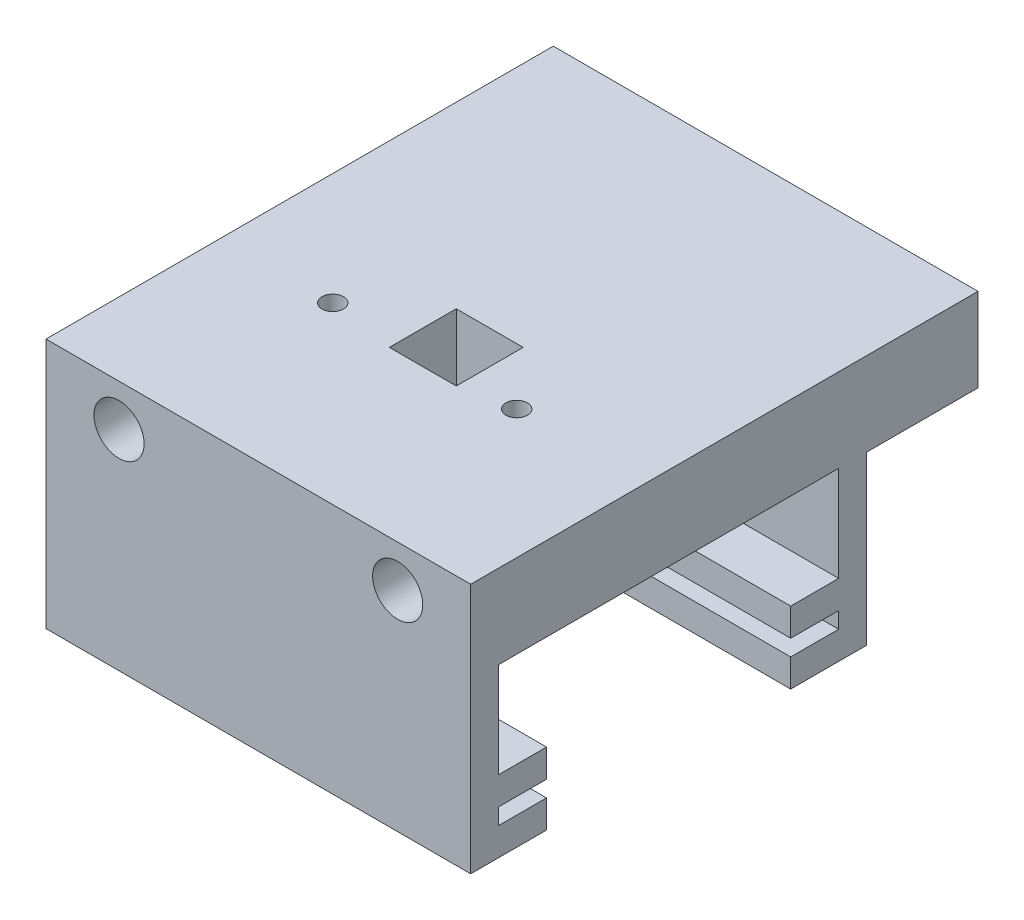
SolidWorks part; units mm, degrees
ref_plane "Front Plane" through (0, 0, 0) normal (0, 0, 1) x (1, 0, 0)
ref_plane "Top Plane" through (0, 0, 0) normal (0, 1, 0) x (1, 0, 0)
ref_plane "Right Plane" through (0, 0, 0) normal (1, 0, 0) x (0, 0, -1)
sketch "Sketch2" plane through (0, 0, 0) normal (0, 0, 1) x (1, 0, 0)
  line L0 (-22, 1.15) -> (3, 1.15) construction
  line L1 (-35.1, 8.65) -> (41.1, 8.65)
  line L2 (-35.1, 8.65) -> (-35.1, -6.35)
  line L3 (-35.1, -6.35) -> (41.1, -6.35)
  line L4 (41.1, 8.65) -> (41.1, -6.35)
  line L12 (3, 1.15) -> (3, 14.1161) construction
  line L13 (3, 1.15) -> (28, 1.15) construction
  circle A0 centre (-22, 1.15) radius 3.9688
  circle A1 centre (28, 1.15) radius 3.9687
  point P2 (3, 8.65)
  dimension "D1" = 7.9375
  dimension "D2" = 7.9375
  dimension "D3" = 15
  dimension "D4" = 50
  dimension "D6" = 76.2
extrude "Top + failed holes" add sketch "Sketch2" against normal blind 71.02
sketch "Sketch8" plane through (-35.1, 0, 0) normal (-1, 0, 0) x (0, 0, 1)
  line L0 (-56.45, 9.45) -> (-56.45, 8.75)
  line L1 (-57.25, 4.65) -> (-17.25, 4.65)
  line L2 (-57.25, 4.65) -> (-57.25, 9.45)
  line L3 (-57.15, 9.55) -> (-56.55, 9.55)
  line L4 (-17.25, 4.65) -> (-17.25, 9.45)
  line L5 (-56.35, 8.65) -> (-55.35, 8.65)
  line L6 (-18.05, 9.45) -> (-18.05, 8.75)
  line L7 (-17.95, 9.55) -> (-17.35, 9.55)
  line L8 (-55.25, 8.75) -> (-55.25, 9.45)
  line L9 (-55.15, 9.55) -> (-54.55, 9.55)
  line L10 (-54.45, 9.45) -> (-54.45, 8.75)
  line L11 (-53.25, 8.75) -> (-53.25, 9.45)
  line L12 (-53.15, 9.55) -> (-52.55, 9.55)
  line L13 (-52.45, 9.45) -> (-52.45, 8.75)
  line L14 (-51.25, 8.75) -> (-51.25, 9.45)
  line L15 (-51.15, 9.55) -> (-50.55, 9.55)
  line L16 (-50.45, 9.45) -> (-50.45, 8.75)
  line L17 (-49.25, 8.75) -> (-49.25, 9.45)
  line L18 (-49.15, 9.55) -> (-48.55, 9.55)
  line L19 (-48.45, 9.45) -> (-48.45, 8.75)
  line L20 (-47.25, 8.75) -> (-47.25, 9.45)
  line L21 (-47.15, 9.55) -> (-46.55, 9.55)
  line L22 (-46.45, 9.45) -> (-46.45, 8.75)
  line L23 (-45.25, 8.75) -> (-45.25, 9.45)
  line L24 (-45.15, 9.55) -> (-44.55, 9.55)
  line L25 (-44.45, 9.45) -> (-44.45, 8.75)
  line L26 (-44.35, 8.65) -> (-30.15, 8.65)
  line L27 (-46.35, 8.65) -> (-45.35, 8.65)
  line L28 (-48.35, 8.65) -> (-47.35, 8.65)
  line L29 (-50.35, 8.65) -> (-49.35, 8.65)
  line L30 (-52.35, 8.65) -> (-51.35, 8.65)
  line L31 (-54.35, 8.65) -> (-53.35, 8.65)
  line L32 (-20.05, 9.45) -> (-20.05, 8.75)
  line L33 (-19.95, 9.55) -> (-19.35, 9.55)
  line L34 (-19.25, 8.75) -> (-19.25, 9.45)
  line L35 (-22.05, 9.45) -> (-22.05, 8.75)
  line L36 (-21.95, 9.55) -> (-21.35, 9.55)
  line L37 (-21.25, 8.75) -> (-21.25, 9.45)
  line L38 (-24.05, 9.45) -> (-24.05, 8.75)
  line L39 (-23.95, 9.55) -> (-23.35, 9.55)
  line L40 (-23.25, 8.75) -> (-23.25, 9.45)
  line L41 (-26.05, 9.45) -> (-26.05, 8.75)
  line L42 (-25.95, 9.55) -> (-25.35, 9.55)
  line L43 (-25.25, 8.75) -> (-25.25, 9.45)
  line L44 (-28.05, 9.45) -> (-28.05, 8.75)
  line L45 (-27.95, 9.55) -> (-27.35, 9.55)
  line L46 (-27.25, 8.75) -> (-27.25, 9.45)
  line L47 (-30.05, 9.45) -> (-30.05, 8.75)
  line L48 (-29.95, 9.55) -> (-29.35, 9.55)
  line L49 (-29.25, 8.75) -> (-29.25, 9.45)
  line L50 (-29.15, 8.65) -> (-28.15, 8.65)
  line L51 (-27.15, 8.65) -> (-26.15, 8.65)
  line L52 (-25.15, 8.65) -> (-24.15, 8.65)
  line L53 (-23.15, 8.65) -> (-22.15, 8.65)
  line L54 (-21.15, 8.65) -> (-20.15, 8.65)
  line L55 (-19.15, 8.65) -> (-18.15, 8.65)
  line L56 (-35.51, 8.65) -> (-35.51, 28.1232) construction
  line L57 (-71.02, 8.65) -> (0, 8.65) construction
  arc A0 (-17.35, 9.55) -> (-17.25, 9.45) centre (-17.35, 9.45) cw
  arc A1 (-18.05, 9.45) -> (-17.95, 9.55) centre (-17.95, 9.45) cw
  arc A2 (-18.15, 8.65) -> (-18.05, 8.75) centre (-18.15, 8.75) ccw
  arc A3 (-19.15, 8.65) -> (-19.25, 8.75) centre (-19.15, 8.75) cw
  arc A4 (-19.35, 9.55) -> (-19.25, 9.45) centre (-19.35, 9.45) cw
  arc A5 (-20.05, 9.45) -> (-19.95, 9.55) centre (-19.95, 9.45) cw
  arc A6 (-20.05, 8.75) -> (-20.15, 8.65) centre (-20.15, 8.75) cw
  arc A7 (-21.15, 8.65) -> (-21.25, 8.75) centre (-21.15, 8.75) cw
  arc A8 (-21.35, 9.55) -> (-21.25, 9.45) centre (-21.35, 9.45) cw
  arc A9 (-22.05, 9.45) -> (-21.95, 9.55) centre (-21.95, 9.45) cw
  arc A10 (-22.05, 8.75) -> (-22.15, 8.65) centre (-22.15, 8.75) cw
  arc A11 (-23.25, 8.75) -> (-23.15, 8.65) centre (-23.15, 8.75) ccw
  arc A12 (-23.35, 9.55) -> (-23.25, 9.45) centre (-23.35, 9.45) cw
  arc A13 (-24.05, 9.45) -> (-23.95, 9.55) centre (-23.95, 9.45) cw
  arc A14 (-24.05, 8.75) -> (-24.15, 8.65) centre (-24.15, 8.75) cw
  arc A15 (-25.25, 8.75) -> (-25.15, 8.65) centre (-25.15, 8.75) ccw
  arc A16 (-25.35, 9.55) -> (-25.25, 9.45) centre (-25.35, 9.45) cw
  arc A17 (-26.05, 9.45) -> (-25.95, 9.55) centre (-25.95, 9.45) cw
  arc A18 (-26.05, 8.75) -> (-26.15, 8.65) centre (-26.15, 8.75) cw
  arc A19 (-27.25, 8.75) -> (-27.15, 8.65) centre (-27.15, 8.75) ccw
  arc A20 (-27.35, 9.55) -> (-27.25, 9.45) centre (-27.35, 9.45) cw
  arc A21 (-28.05, 9.45) -> (-27.95, 9.55) centre (-27.95, 9.45) cw
  arc A22 (-28.05, 8.75) -> (-28.15, 8.65) centre (-28.15, 8.75) cw
  arc A23 (-29.25, 8.75) -> (-29.15, 8.65) centre (-29.15, 8.75) ccw
  arc A24 (-29.35, 9.55) -> (-29.25, 9.45) centre (-29.35, 9.45) cw
  arc A25 (-30.05, 9.45) -> (-29.95, 9.55) centre (-29.95, 9.45) cw
  arc A26 (-30.05, 8.75) -> (-30.15, 8.65) centre (-30.15, 8.75) cw
  arc A27 (-44.45, 8.75) -> (-44.35, 8.65) centre (-44.35, 8.75) ccw
  arc A28 (-44.55, 9.55) -> (-44.45, 9.45) centre (-44.55, 9.45) cw
  arc A29 (-45.25, 8.75) -> (-45.35, 8.65) centre (-45.35, 8.75) cw
  arc A30 (-45.25, 9.45) -> (-45.15, 9.55) centre (-45.15, 9.45) cw
  arc A31 (-46.45, 8.75) -> (-46.35, 8.65) centre (-46.35, 8.75) ccw
  arc A32 (-46.55, 9.55) -> (-46.45, 9.45) centre (-46.55, 9.45) cw
  arc A33 (-47.25, 9.45) -> (-47.15, 9.55) centre (-47.15, 9.45) cw
  arc A34 (-47.25, 8.75) -> (-47.35, 8.65) centre (-47.35, 8.75) cw
  arc A35 (-48.45, 8.75) -> (-48.35, 8.65) centre (-48.35, 8.75) ccw
  arc A36 (-48.55, 9.55) -> (-48.45, 9.45) centre (-48.55, 9.45) cw
  arc A37 (-49.25, 8.75) -> (-49.35, 8.65) centre (-49.35, 8.75) cw
  arc A38 (-49.25, 9.45) -> (-49.15, 9.55) centre (-49.15, 9.45) cw
  arc A39 (-50.45, 8.75) -> (-50.35, 8.65) centre (-50.35, 8.75) ccw
  arc A40 (-50.55, 9.55) -> (-50.45, 9.45) centre (-50.55, 9.45) cw
  arc A41 (-51.25, 8.75) -> (-51.35, 8.65) centre (-51.35, 8.75) cw
  arc A42 (-51.25, 9.45) -> (-51.15, 9.55) centre (-51.15, 9.45) cw
  arc A43 (-52.45, 8.75) -> (-52.35, 8.65) centre (-52.35, 8.75) ccw
  arc A44 (-52.55, 9.55) -> (-52.45, 9.45) centre (-52.55, 9.45) cw
  arc A45 (-53.25, 8.75) -> (-53.35, 8.65) centre (-53.35, 8.75) cw
  arc A46 (-53.25, 9.45) -> (-53.15, 9.55) centre (-53.15, 9.45) cw
  arc A47 (-54.45, 8.75) -> (-54.35, 8.65) centre (-54.35, 8.75) ccw
  arc A48 (-54.55, 9.55) -> (-54.45, 9.45) centre (-54.55, 9.45) cw
  arc A49 (-55.25, 8.75) -> (-55.35, 8.65) centre (-55.35, 8.75) cw
  arc A50 (-55.25, 9.45) -> (-55.15, 9.55) centre (-55.15, 9.45) cw
  arc A51 (-56.45, 8.75) -> (-56.35, 8.65) centre (-56.35, 8.75) ccw
  arc A52 (-56.45, 9.45) -> (-56.55, 9.55) centre (-56.55, 9.45) ccw
  arc A53 (-57.25, 9.45) -> (-57.15, 9.55) centre (-57.15, 9.45) cw
  point P165 (-37.25, 8.65)
  dimension "D1" = 0.1
  dimension "D2" = 14.2
sketch "Sketch13" plane through (0, 8.65, 0) normal (0, 1, 0) x (1, 0, 0)
  line L0 (41.1, 71.02) -> (41.1, 0) construction
  line L1 (-35.1, 71.02) -> (41.1, 71.02)
  line L3 (-30.1, 66.02) -> (41.1, 66.02)
  line L4 (41.1, 71.02) -> (41.1, 66.02)
  line L5 (-35.1, 0) -> (41.1, 0) construction
  line L7 (-35.1, 71.02) -> (-35.1, 0)
  line L9 (-30.1, 66.02) -> (-30.1, 5)
  line L11 (-35.1, 0) -> (41.1, 0)
  line L13 (-30.1, 5) -> (41.1, 5)
  line L14 (41.1, 0) -> (41.1, 5)
  dimension "D1" = 5
  dimension "D2" = 5
  dimension "D3" = 5
extrude "Walls" add sketch "Sketch13" against normal blind 45
sketch "Sketch14" plane through (0, 0, 0) normal (0, 0, 1) x (1, 0, 0)
  line L0 (-22, 1.15) -> (3, 1.15) construction
  line L1 (-35.1, 8.65) -> (41.1, 8.65)
  line L2 (-35.1, 8.65) -> (-35.1, -6.35)
  line L3 (-35.1, -6.35) -> (41.1, -6.35)
  line L4 (41.1, 8.65) -> (41.1, -6.35)
  line L5 (3, 1.15) -> (3, 14.1161) construction
  line L6 (3, 1.15) -> (28, 1.15) construction
  circle A0 centre (-22, 1.15) radius 4.5
  circle A1 centre (28, 1.15) radius 4.5
  point P2 (3, 8.65)
  dimension "D1" = 9
  dimension "D2" = 9
  dimension "D3" = 15
  dimension "D4" = 50
  dimension "D5" = 76.2
extrude "Rod Holes" cut sketch "Sketch14" against normal through all contours A0 | A1
sketch "Sketch15" plane through (0, -36.35, 0) normal (0, -1, 0) x (1, 0, 0)
  line L0 (-35.1, -35.51) -> (41.1, -35.51) construction
  line L1 (-35.1, 0) -> (41.1, 0)
  line L2 (-35.1, 0) -> (-35.1, -71.02)
  line L3 (-35.1, -71.02) -> (41.1, -71.02)
  line L4 (41.1, 0) -> (41.1, -71.02)
  line L5 (-35.1, 0) -> (41.1, 0)
  line L6 (-35.1, 0) -> (-35.1, -12.0833)
  line L8 (41.1, 0) -> (41.1, -12.0833)
  line L9 (-35.1, -71.02) -> (41.1, -71.02)
  line L10 (-35.1, -71.02) -> (-35.1, -57.415)
  line L11 (-35.1, -57.415) -> (41.1, -57.415)
  line L12 (41.1, -71.02) -> (41.1, -57.415)
  line L13 (-35.1, -13.605) -> (41.1, -13.605)
  line L14 (41.1, 0) -> (41.1, -13.605)
  line L15 (-35.1, 0) -> (41.1, 0)
  line L16 (-35.1, 0) -> (-35.1, -13.605)
  line M1 (41.1, -71.02) -> (41.1, -66.02)
  line M2 (41.1, -66.02) -> (-30.1, -66.02)
  line M3 (-30.1, -66.02) -> (-30.1, -5)
  line M4 (-30.1, -5) -> (41.1, -5)
  line M5 (41.1, -5) -> (41.1, 0)
  line M6 (41.1, 0) -> (-35.1, 0)
  line M7 (-35.1, 0) -> (-35.1, -71.02)
  line M8 (-35.1, -71.02) -> (41.1, -71.02)
  dimension "D1" = 43.81
extrude "Base hold syringe" add sketch "Sketch15" against normal blind 5 contours L13 L4 M3 M4 | L2 L13 M3 M4 M5 M6 M7 | L11 L4 M3 M2 | L11 M7 M8 M1 M2 M3
sketch "Sketch16" plane through (0, 0, -71.02) normal (0, 0, -1) x (-1, 0, 0)
  line L0 (-28, 1.15) -> (-3, 1.15) construction
  line L1 (-41.1, 8.65) -> (35.1, 8.65)
  line L2 (-41.1, 8.65) -> (-41.1, -6.35)
  line L3 (-41.1, -6.35) -> (35.1, -6.35)
  line L4 (35.1, 8.65) -> (35.1, -6.35)
  line L5 (-3, 1.15) -> (-3, 14.1161) construction
  line L6 (-3, 1.15) -> (22, 1.15) construction
  circle A0 centre (-28, 1.15) radius 4.5
  circle A1 centre (22, 1.15) radius 4.5
  point P2 (-3, 8.65)
  dimension "D1" = 9
  dimension "D2" = 9
  dimension "D3" = 15
  dimension "D4" = 50
  dimension "D5" = 76.2
extrude "extension for motor" add sketch "Sketch16" along normal blind 20
sketch "Sketch6" plane through (0, 8.65, 0) normal (0, 1, 0) x (1, 0, 0)
  line L0 (41.1, 71.02) -> (-35.1, 71.02) construction
  line L6 (3, 41.51) -> (3, 29.51) construction
  line L7 (41.1, 71.02) -> (-35.1, 71.02)
  line L8 (-35.1, 0) -> (41.1, 0) construction
  line L17 (3, 71.02) -> (3, 0) construction
  line L18 (-35.1, 0) -> (41.1, 0)
  line L20 (38.47, 48.51) -> (38.47, 21.19)
  line L27 (9, 41.51) -> (-3, 41.51)
  line L28 (9, 29.51) -> (9, 41.51)
  line L29 (-3, 29.51) -> (9, 29.51)
  line L30 (-27.57, 48.51) -> (38.47, 48.51)
  line L31 (-27.57, 21.19) -> (-27.57, 48.51)
  line L32 (38.47, 21.19) -> (-27.57, 21.19)
  line L33 (-3, 41.51) -> (-3, 29.51)
  line L34 (18, 41.51) -> (18, 21.19) construction
  line L35 (-15, 41.51) -> (-15, 21.19) construction
  line L36 (-15, 41.51) -> (18, 41.51) construction
  circle A7 centre (18, 31.35) radius 1.925
  circle A8 centre (-15, 31.35) radius 1.925
  circle A9 centre (3, 35.51) radius 21.905
  point P0 (3, 35.51)
  point P1 (3, 35.51)
  point P4 (-15, 31.35)
  point P5 (18, 31.35)
  point P11 (11.9104, 37.25)
  point P13 (3, 71.02)
  dimension "D3" = 3.85
  dimension "D4" = 43.81
  dimension "D5" = 3.85
  dimension "D10" = 9
  dimension "D2" = 12
  dimension "D6" = 12
  dimension "D7" = 12
  dimension "D8" = 66.04
  dimension "D9" = 27.32
  dimension "D12" = 24.57
  dimension "D14" = 20.32
  dimension "D15" = 7
extrude "Track and screws" cut sketch "Sketch6" against normal up to next
sketch "Sketch17" plane through (0, 8.65, 0) normal (0, 1, 0) x (1, 0, 0)
  line L3 (-2.03, 88.71) -> (41.1, 88.71)
  line L4 (-2.03, 88.71) -> (-2.03, 91.02)
  line L5 (-2.03, 91.02) -> (41.1, 91.02)
  line L6 (41.1, 88.71) -> (41.1, 91.02)
  line L7 (-35.1, 91.02) -> (41.1, 91.02) construction
  line L8 (41.1, 91.02) -> (41.1, 0) construction
  line L9 (9, 41.51) -> (-3, 41.51) construction
  dimension "D2" = 47.2
sketch "Sketch18" plane through (41.1, 0, 0) normal (1, 0, 0) x (0, 0, -1)
  line L0 (5, -31.35) -> (5, -6.35) construction
  line L1 (5, -28.45) -> (13.605, -28.45)
  line L2 (5, -28.45) -> (5, -23.45)
  line L3 (5, -23.45) -> (13.605, -23.45)
  line L4 (13.605, -28.45) -> (13.605, -23.45)
  line L5 (66.02, -31.35) -> (66.02, -6.35) construction
  line L6 (66.02, -28.45) -> (57.415, -28.45)
  line L7 (66.02, -28.45) -> (66.02, -23.45)
  line L8 (66.02, -23.45) -> (57.415, -23.45)
  line L9 (57.415, -28.45) -> (57.415, -23.45)
  line L10 (5, -31.35) -> (13.605, -31.35) construction
  line L11 (13.605, -31.35) -> (13.605, -36.35) construction
  line L12 (57.415, -36.35) -> (57.415, -31.35) construction
  dimension "D1" = 2.9
  dimension "D2" = 5
extrude "Secure syring" add sketch "Sketch18" against normal up to next
ref_plane "Plane1" through (-35.1, 8.65, -91.02) normal (0, 0, 1) x (1, 0, 0)
sketch "Sketch21" plane through (-35.1, 0, 0) normal (-1, 0, 0) x (0, 0, 1)
  line L0 (-91.02, 8.65) -> (0, 8.65) construction
  line L1 (-91.02, 8.65) -> (0, 8.65)
  line L2 (-71.02, -18.6219) -> (0, -18.6219) construction
  line L3 (-35.51, -18.6219) -> (-35.51, -13.8018) construction
  line L4 (-45.51, -18.6219) -> (-25.51, -18.6219) construction
  line L5 (-45.51, -8.3338) -> (-25.51, -8.3338)
  line L6 (-45.51, -28.91) -> (-25.51, -28.91)
  line L8 (-71.02, -36.35) -> (0, -36.35)
  line L9 (0, -36.35) -> (0, 8.65)
  line L10 (0, 8.65) -> (-91.02, 8.65)
  line L11 (-91.02, 8.65) -> (-91.02, -6.35)
  line L12 (-91.02, -6.35) -> (-71.02, -6.35)
  line L13 (-71.02, -6.35) -> (-71.02, -36.35)
  line L14 (-71.02, -36.35) -> (0, -36.35)
  line L15 (0, -36.35) -> (0, 8.65)
  line L16 (0, 8.65) -> (-91.02, 8.65)
  line L17 (-91.02, 8.65) -> (-91.02, -6.35)
  line L18 (-91.02, -6.35) -> (-71.02, -6.35)
  line L19 (-71.02, -6.35) -> (-71.02, -36.35)
  arc A0 (-45.51, -8.3338) -> (-45.51, -28.91) centre (-45.51, -18.6219) ccw
  arc A1 (-25.51, -28.91) -> (-25.51, -8.3338) centre (-25.51, -18.6219) ccw
  point P8 (-45.51, -18.6219)
  point P10 (-25.51, -18.6219)
  point P14 (-35.51, -18.6219)
  dimension "D2" = 20
  dimension "D1" = 0
extrude "Cut-Extrude1" cut sketch "Sketch21" against normal up to next contours L6 A1 L5 A0
sketch "Sketch22" plane through (0, -36.35, 0) normal (0, -1, 0) x (1, 0, 0)
  line L0 (9, -41.51) -> (-3, -41.51) construction
  line L1 (9, -29.51) -> (9, -41.51) construction
  line L2 (9, -41.51) -> (-3, -41.51)
  line L3 (9, -29.51) -> (9, -41.51)
  line L4 (9, -41.51) -> (9, -29.51)
  line L5 (-3, -41.51) -> (9, -41.51)
  line L6 (-3, -29.51) -> (-3, -41.51)
  line L7 (9, -29.51) -> (-3, -29.51)
  line L8 (9, -41.51) -> (9, -29.51)
  line L9 (-3, -41.51) -> (9, -41.51)
  line L10 (-3, -29.51) -> (-3, -41.51)
  line L11 (9, -29.51) -> (-3, -29.51)
  line L12 (3, -29.51) -> (3, -41.51) construction
  line L13 (-19, -57.415) -> (-19, -13.605)
  line L14 (-19, -13.605) -> (-30.1, -13.605)
  line L16 (-30.1, -57.415) -> (-19, -57.415)
  line L17 (-30.1, -13.605) -> (-30.1, -57.415) construction
  line L18 (-30.1, -13.605) -> (-30.1, -57.415)
  line L19 (-30.1, -13.605) -> (41.1, -13.605) construction
  line L20 (-30.1, -57.415) -> (41.1, -57.415) construction
  circle A0 centre (3, -35.51) radius 22
  point P14 (-19, -35.51)
  dimension "D2" = 44
  dimension "D1" = 0
extrude "Boss-Extrude1" add sketch "Sketch22" against normal blind 5 separate body contours L16 L13 L14 L18
